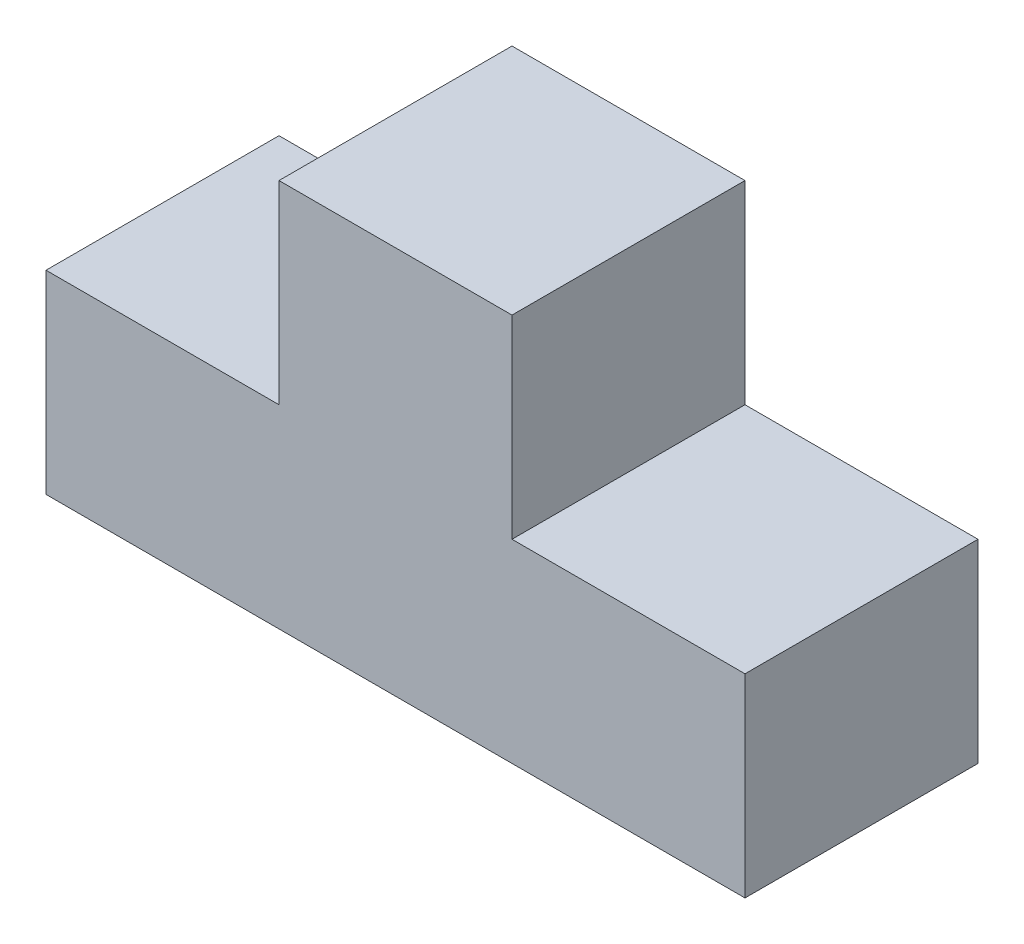
SolidWorks part; units mm, degrees
ref_plane "Front Plane" through (0, 0, 0) normal (0, 0, 1) x (1, 0, 0)
ref_plane "Top Plane" through (0, 0, 0) normal (0, 1, 0) x (1, 0, 0)
ref_plane "Right Plane" through (0, 0, 0) normal (1, 0, 0) x (0, 0, -1)
sketch "Sketch1" plane through (0, 0, 0) normal (0, 0, 1) x (1, 0, 0)
  line L0 (0, 0) -> (90, 0)
  line L1 (90, 0) -> (90, 25)
  line L2 (90, 25) -> (60, 25)
  line L3 (60, 25) -> (60, 50)
  line L4 (60, 50) -> (30, 50)
  line L5 (30, 50) -> (30, 25)
  line L6 (30, 25) -> (0, 25)
  line L7 (0, 25) -> (0, 0)
  dimension "D1" = 90
  dimension "D2" = 25
  dimension "D3" = 30
  dimension "D4" = 25
  dimension "D5" = 30
  dimension "D6" = 25
extrude "Boss-Extrude1" add sketch "Sketch1" along normal blind 30
